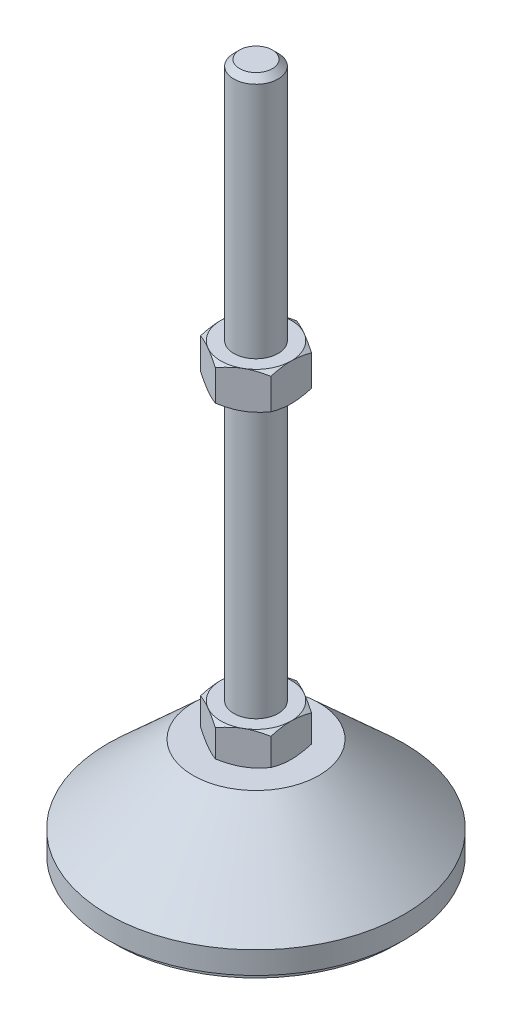
SolidWorks part; units mm, degrees
ref_plane "Спереди" through (0, 0, 0) normal (0, 0, 1) x (1, 0, 0)
ref_plane "Сверху" through (0, 0, 0) normal (0, 1, 0) x (1, 0, 0)
ref_plane "Справа" through (0, 0, 0) normal (1, 0, 0) x (0, 0, -1)
sketch "Эскиз1" plane through (0, 0, 0) normal (0, 0, 1) x (1, 0, 0)
  line L0 (0, 0) -> (-38, 0)
  line L1 (-38, 0) -> (-38, 2)
  line L2 (-38, 2) -> (-40, 2)
  line L3 (-40, 2) -> (-40, 8)
  line L4 (-40, 8) -> (-17, 29)
  line L5 (-17, 29) -> (-6, 29)
  line L12 (-6, 38) -> (-6, 186.4)
  line L13 (-6, 186.4) -> (-4.4, 188)
  line L14 (-4.4, 188) -> (0, 188)
  line L15 (0, 188) -> (0, 0) construction
  line L16 (-6, 29) -> (0, 29) construction
  line L17 (0, 0) -> (0, 188)
  line L18 (0, 0) -> (0, -7.9595) construction
  line L19 (-6, 38) -> (-6, 29)
  point P8 (-6, 112.2)
  point P23 (-11.5, 29)
  dimension "D1" = 12
  dimension "D2" = 29
  dimension "D3" = 9
  dimension "D4" = 80
  dimension "D5" = 6
  dimension "D6" = 1.6
  dimension "D7" = 45
  dimension "D8" = 34
  dimension "D9" = 2
  dimension "D10" = 150
  dimension "D11" = 6
revolve "Повернуть1" add sketch "Эскиз1" angle 360 about L17
sketch "Эскиз2" plane through (0, 29, 0) normal (0, 1, 0) x (1, 0, 0)
  line L1 (0, 10.9697) -> (-9.5, 5.4848)
  line L2 (-9.5, 5.4848) -> (-9.5, -5.4848)
  line L3 (-9.5, -5.4848) -> (0, -10.9697)
  line L4 (0, -10.9697) -> (9.5, -5.4848)
  line L5 (9.5, -5.4848) -> (9.5, 5.4848)
  line L6 (9.5, 5.4848) -> (0, 10.9697)
  circle A0 centre (0, 0) radius 9.5 construction
  dimension "D1" = 19
extrude "Бобышка-Вытянуть1" add sketch "Эскиз2" along normal up to vertex (9 mm away) up to point (-6, 38, 0)
ref_plane "Плоскость1" through (0, 112.2, 0) normal (0, 1, 0) x (1, 0, 0)
sketch "Эскиз3" plane through (0, 112.2, 0) normal (0, 1, 0) x (1, 0, 0)
  line L6 (9.5, 5.4848) -> (0, 10.9697)
  line L7 (0, 10.9697) -> (-9.5, 5.4848)
  line L8 (-9.5, 5.4848) -> (-9.5, -5.4848)
  line L9 (-9.5, -5.4848) -> (0, -10.9697)
  line L10 (0, -10.9697) -> (9.5, -5.4848)
  line L11 (9.5, -5.4848) -> (9.5, 5.4848)
  line L12 (9.5, 5.4848) -> (0, 10.9697)
  line L13 (0, 10.9697) -> (-9.5, 5.4848)
  line L14 (-9.5, 5.4848) -> (-9.5, -5.4848)
  line L15 (-9.5, -5.4848) -> (0, -10.9697)
  line L16 (0, -10.9697) -> (9.5, -5.4848)
  line L17 (9.5, -5.4848) -> (9.5, 5.4848)
  dimension "D1" = 0
extrude "Бобышка-Вытянуть2" add sketch "Эскиз3" along normal blind 10
sketch "Эскиз4" plane through (0, 0, 0) normal (0, 0, 1) x (1, 0, 0)
  line L0 (-9.5, 122.2) -> (-18.1603, 117.2)
  line L1 (-18.1603, 117.2) -> (-18.1603, 122.2)
  line L2 (-18.1603, 122.2) -> (-9.5, 122.2)
  line L3 (-18.1603, 117.2) -> (-9.5, 112.2)
  line L4 (50, 112.2) -> (-50, 112.2) construction
  line L5 (-9.5, 112.2) -> (-18.1603, 112.2)
  line L6 (-18.1603, 112.2) -> (-18.1603, 117.2)
  line L7 (-9.5, 122.2) -> (-9.5, 112.2) construction
  line L8 (-9.5, 38) -> (-17.2942, 38)
  line L9 (-17.2942, 38) -> (-17.2942, 33.5)
  line L10 (-17.2942, 33.5) -> (-9.5, 38)
  line L11 (-9.5, 29) -> (-17.2942, 33.5)
  line L12 (-17.2942, 33.5) -> (-17.2942, 29)
  line L13 (-17.2942, 29) -> (-9.5, 29)
  line L14 (0, 188) -> (0, 96.3793) construction
  dimension "D1" = 30
  dimension "D2" = 30
revolve "Вырез-Повернуть2" cut sketch "Эскиз4" angle 360 about L14
